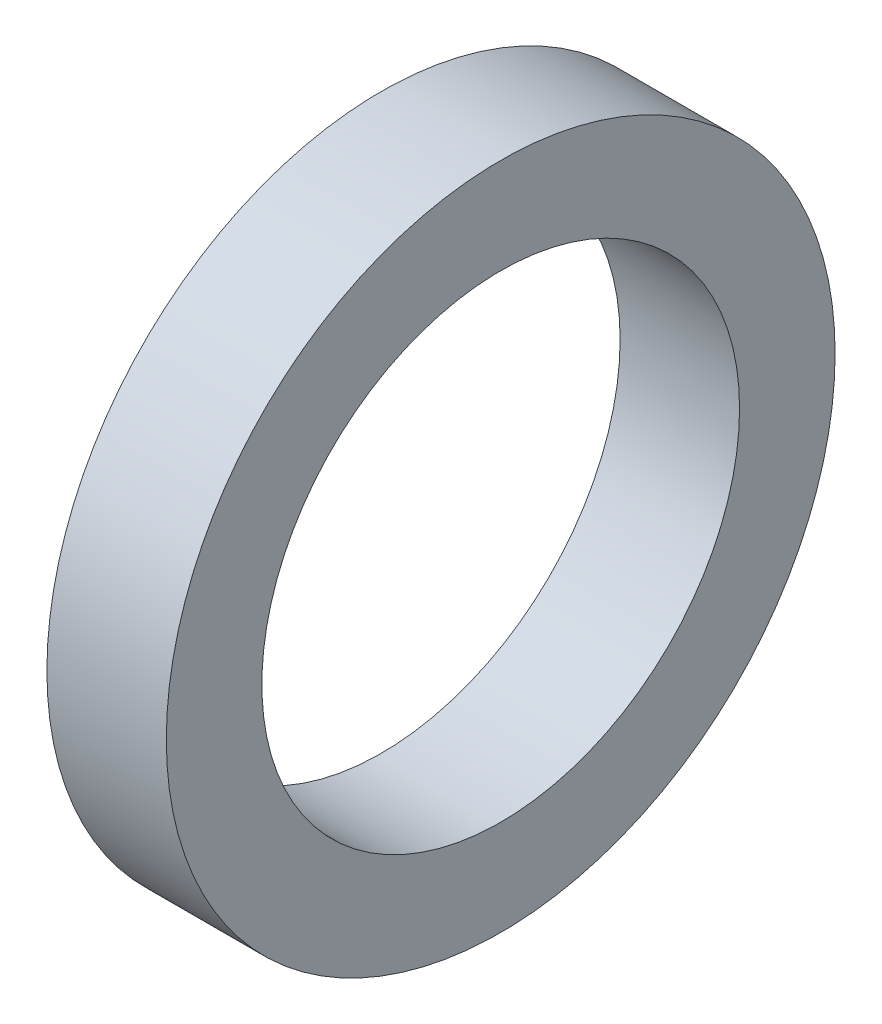
SolidWorks part; units mm, degrees
ref_plane "Front Plane" through (0, 0, 0) normal (0, 0, 1) x (1, 0, 0)
ref_plane "Top Plane" through (0, 0, 0) normal (0, 1, 0) x (1, 0, 0)
ref_plane "Right Plane" through (0, 0, 0) normal (1, 0, 0) x (0, 0, -1)
sketch "Sketch1" plane through (0, 0, 0) normal (1, 0, 0) x (0, 0, -1)
  circle A0 centre (0, 0) radius 6.35
  circle A1 centre (0, 0) radius 8.89
  dimension "D1" = 12.7
  dimension "D2" = 2.54
extrude "Boss-Extrude1" add sketch "Sketch1" along normal blind 3.175
